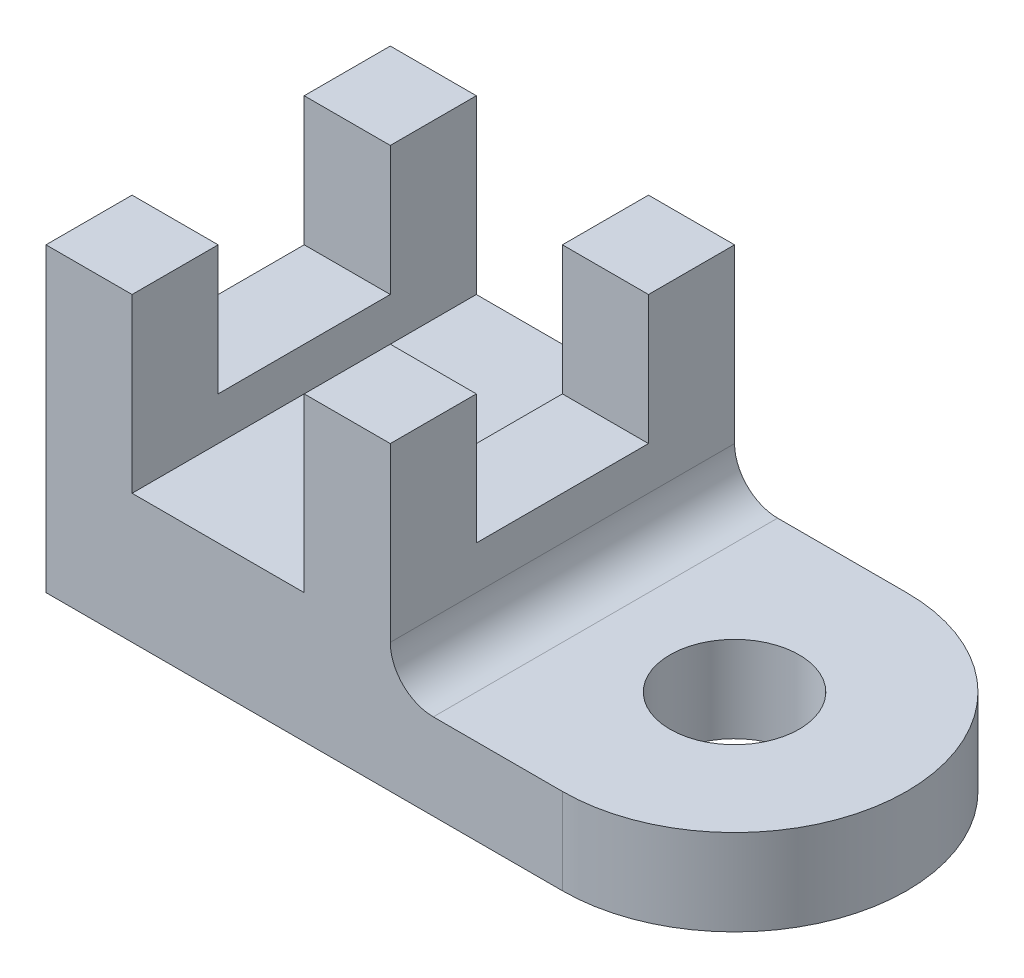
SolidWorks part; units mm, degrees
material "1060 Alloy"
ref_plane "Front Plane" through (0, 0, 0) normal (0, 0, 1) x (1, 0, 0)
ref_plane "Top Plane" through (0, 0, 0) normal (0, 1, 0) x (1, 0, 0)
ref_plane "Right Plane" through (0, 0, 0) normal (1, 0, 0) x (0, 0, -1)
sketch "base" plane through (0, 0, 0) normal (0, 0, 1) x (1, 0, 0)
  line L0 (-38.1, 0) -> (38.1, 0)
  line L1 (38.1, 0) -> (38.1, 12.7)
  line L2 (38.1, 12.7) -> (19.05, 12.7)
  line L3 (12.7, 19.05) -> (12.7, 44.45)
  line L4 (12.7, 44.45) -> (0, 44.45)
  line L5 (0, 44.45) -> (0, 19.05)
  line L6 (0, 19.05) -> (-25.4, 19.05)
  line L7 (-25.4, 19.05) -> (-25.4, 44.45)
  line L8 (-25.4, 44.45) -> (-38.1, 44.45)
  line L9 (-38.1, 44.45) -> (-38.1, 0)
  arc A0 (12.7, 19.05) -> (19.05, 12.7) centre (19.05, 19.05) ccw
  point P3 (0, 0)
  point P12 (0, 0)
  dimension "D8" = 6.35
  dimension "D1" = 44.45
  dimension "D2" = 76.2
  dimension "D3" = 12.7
  dimension "D4" = 19.05
  dimension "D5" = 12.7
  dimension "D6" = 12.7
  dimension "D7" = 50.8
extrude "baseExtrude" add sketch "base" along normal mid plane 50.8
sketch "Sketch2" plane through (0, 0, 0) normal (0, -1, 0) x (1, 0, 0)
  line L0 (38.1, 25.4) -> (38.1, -25.4) construction
  circle A0 centre (38.1, 0) radius 25.4
extrude "Boss-Extrude2" add sketch "Sketch2" against normal up to surface (12.7 mm away) up to face at (28.575, 12.7, 0)
hole_wizard "3/4 (0.75) Diameter Hole2" positions "Sketch7" profile "Sketch8" hole size "3/4" standard "ANSI Inch" end condition through all
sketch "Sketch7" plane through (0, 12.7, 0) normal (0, 1, 0) x (1, 0, 0)
  point P0 (38.1, 0)
sketch "Sketch8" plane through (38.1, 12.7, 0) normal (1, 0, 0) x (0, 0, 1)
  line L0 (0, 0) -> (0, 12.7)
  line L1 (0, 12.7) -> (9.525, 12.7)
  line L2 (9.525, 12.7) -> (9.525, 0)
  line L5 (9.525, 0) -> (0, 0)
  line L11 (0, -6.35) -> (0, 107.95) construction
  dimension "Thru Hole Dia." = 19.05
  dimension "Thru Hole Depth" = 12.7
sketch "Sketch9" plane through (12.7, 0, 0) normal (1, 0, 0) x (0, 0, -1)
  line L0 (-25.4, 44.45) -> (25.4, 44.45) construction
  line L1 (-12.7, 44.45) -> (12.7, 44.45)
  line L2 (-12.7, 44.45) -> (-12.7, 25.4)
  line L3 (-12.7, 25.4) -> (12.7, 25.4)
  line L4 (12.7, 44.45) -> (12.7, 25.4)
  dimension "D1" = 19.05
  dimension "D2" = 25.4
  dimension "D3" = 12.7
extrude "Cut-Extrude1" cut sketch "Sketch9" against normal through all contours L3 L4 L1 L2
